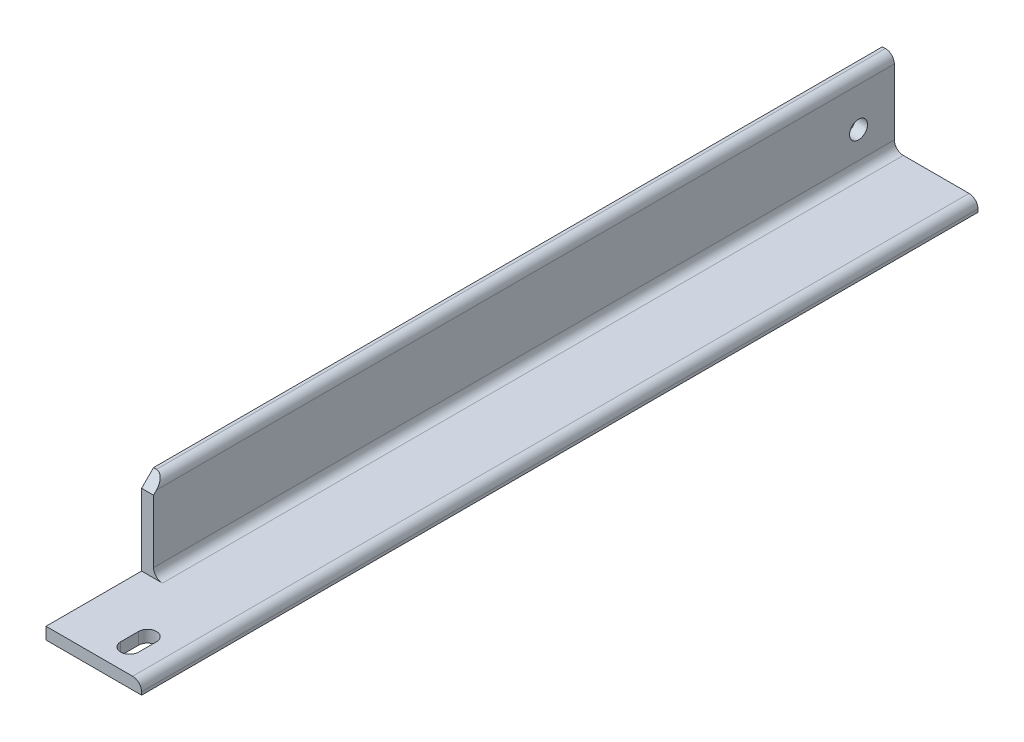
SolidWorks part; units mm, degrees
ref_plane "Front Plane" through (0, 0, 0) normal (0, 0, 1) x (1, 0, 0)
ref_plane "Top Plane" through (0, 0, 0) normal (0, 1, 0) x (1, 0, 0)
ref_plane "Right Plane" through (0, 0, 0) normal (1, 0, 0) x (0, 0, -1)
sketch "Sketch1" plane through (0, 0, 0) normal (0, 0, 1) x (1, 0, 0)
  line L0 (0, 0) -> (0, 101.6)
  line L1 (0, 101.6) -> (3.1801, 101.6)
  line L2 (12.7, 92.0801) -> (12.7, 22.225)
  line L3 (22.225, 12.7) -> (92.0801, 12.7)
  line L4 (101.6, 3.1801) -> (101.6, 0)
  line L5 (101.6, 0) -> (0, 0)
  arc A0 (101.6, 3.1801) -> (92.0801, 12.7) centre (92.0801, 3.1801) ccw
  arc A1 (3.1801, 101.6) -> (12.7, 92.0801) centre (3.1801, 92.0801) cw
  arc A2 (22.225, 12.7) -> (12.7, 22.225) centre (22.225, 22.225) cw
  circle A3 centre (0, 0) radius 9.525 construction
  dimension "D2" = 3.1801
  dimension "Radius_1" = 9.525
  dimension "Radius_2" = 9.525
  dimension "D1" = 12.7
  dimension "V_leg" = 101.6
  dimension "H_leg" = 101.6
  dimension "Thickness" = 12.7
  dimension "Flat_wid" = 3.1801
extrude "Boss-Extrude1" add sketch "Sketch1" along normal mid plane 889
sketch "Sketch2" plane through (0, 0, 0) normal (1, 0, 0) x (0, 1, 0)
  line L0 (101.6, 444.5) -> (101.6, -444.5) construction
  line L1 (12.7, 444.5) -> (12.7, 342.9)
  line L2 (12.7, 342.9) -> (88.9, 342.9)
  line L3 (101.6, 444.5) -> (0, 444.5) construction
  line L4 (12.7, 444.5) -> (101.6, 444.5)
  line L5 (101.6, 444.5) -> (101.6, 342.9)
  line L6 (0, 444.5) -> (0, -444.5) construction
  line L7 (88.9, 342.9) -> (101.6, 330.2)
  line L8 (101.6, 330.2) -> (101.6, 342.9)
  dimension "D1" = 12.7
  dimension "D2" = 12.7
  dimension "D3" = 101.6
  dimension "D4" = 12.7
sketch "Sketch3" plane through (0, 0, 0) normal (0, 1, 0) x (0, 0, 1)
  line L0 (419.1, 63.5) -> (400.05, 63.5) construction
  line L1 (419.1, 53.975) -> (400.05, 53.975)
  line L2 (419.1, 73.025) -> (400.05, 73.025)
  line L5 (444.5, 0) -> (444.5, 101.6) construction
  arc A0 (419.1, 53.975) -> (419.1, 73.025) centre (419.1, 63.5) ccw
  arc A1 (400.05, 73.025) -> (400.05, 53.975) centre (400.05, 63.5) ccw
  point P2 (409.575, 63.5)
  dimension "D1" = 9.525
  dimension "D2" = 38.1
  dimension "D3" = 19.05
  dimension "D4" = 25.4
extrude "Cut-Extrude4" cut sketch "Sketch2" along normal up to next
extrude "Cut-Extrude2" cut sketch "Sketch3" along normal up to next
hole_wizard "3/4 (0.75) Diameter Hole2" positions "Sketch7" profile "Sketch6" hole size "3/4" standard "Ansi Inch" end condition up to next
sketch "Sketch7" plane through (0, 0, 0) normal (-1, 0, 0) x (0, 0, 1)
  line L0 (444.5, 0) -> (-444.5, 0) construction
  line L1 (-444.5, 101.6) -> (-444.5, 0) construction
  point P0 (-406.4, 50.8)
  dimension "D1" = 50.8
  dimension "D2" = 38.1
sketch "Sketch6" plane through (0, 50.8, -406.4) normal (0, 1, 0) x (0, 0, 1)
  line L0 (0, 0) -> (0, 12.7)
  line L1 (0, 12.7) -> (9.525, 12.7)
  line L2 (9.525, 12.7) -> (9.525, 0)
  line L5 (9.525, 0) -> (0, 0)
  line L11 (0, -6.35) -> (0, 107.95) construction
  dimension "Thru Hole Dia." = 19.05
  dimension "Thru Hole Depth" = 12.7
